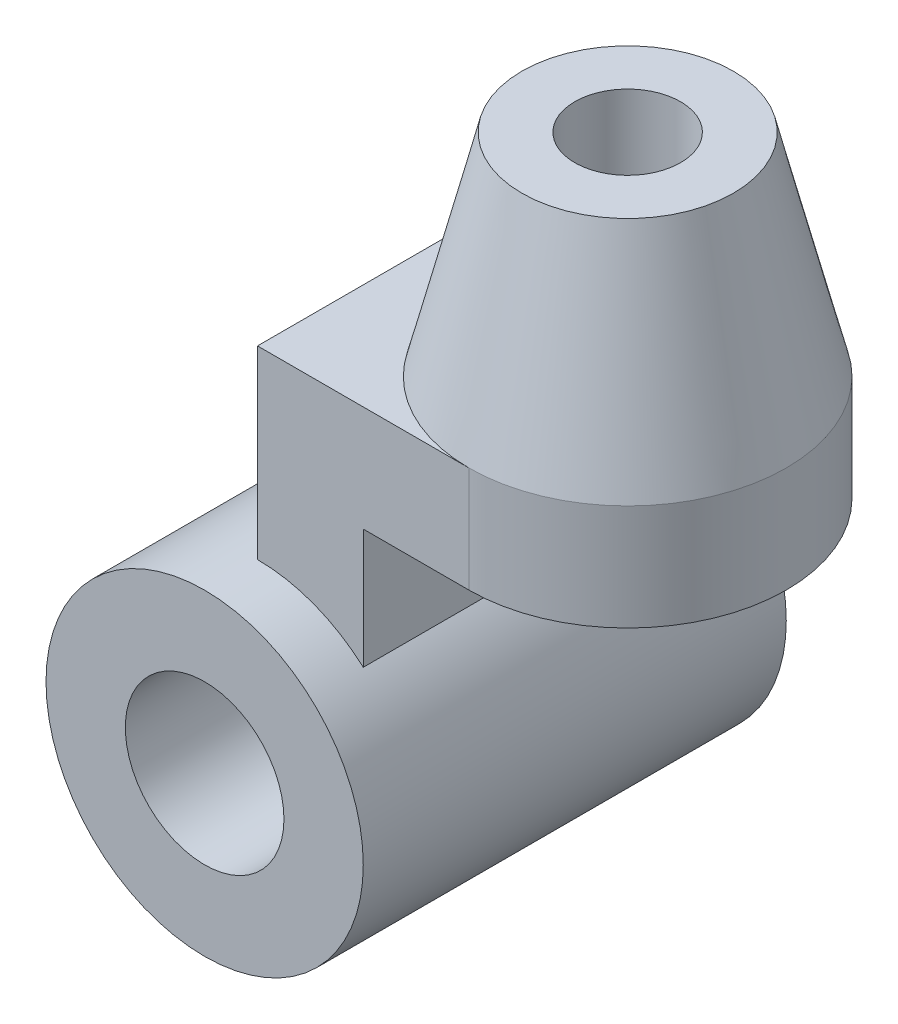
SolidWorks part; units mm, degrees
ref_plane "Front Plane" through (0, 0, 0) normal (0, 0, 1) x (1, 0, 0)
ref_plane "Top Plane" through (0, 0, 0) normal (0, 1, 0) x (1, 0, 0)
ref_plane "Right Plane" through (0, 0, 0) normal (1, 0, 0) x (0, 0, -1)
sketch "Sketch1" plane through (0, 0, 0) normal (0, 0, 1) x (1, 0, 0)
  circle A0 centre (0, 0) radius 300
  circle A1 centre (0, 0) radius 150
  dimension "D1" = 600
  dimension "D2" = 300
extrude "Boss-Extrude1" add sketch "Sketch1" along normal mid plane 800
sketch "Sketch2" plane through (0, 0, 0) normal (0, 0, 1) x (1, 0, 0)
  line L0 (0, 300) -> (0, 650)
  line L1 (0, 650) -> (400, 650)
  line L2 (200, 450) -> (200, 223.6068)
  line L3 (400, 650) -> (400, 450)
  line L4 (400, 450) -> (200, 450)
  circle A0 centre (0, 0) radius 300 construction
  arc A1 (200, 223.6068) -> (0, 300) centre (0, 0) ccw
  dimension "D1" = 350
  dimension "D2" = 200
  dimension "D3" = 400
  dimension "D4" = 200
extrude "Boss-Extrude2" add sketch "Sketch2" along normal mid plane 600
sketch "Sketch5" plane through (0, 0, 0) normal (0, 0, 1) x (1, 0, 0)
  line L0 (400, 1046.5475) -> (400, -75.9294) construction
  line L1 (400, 450) -> (400, 650) construction
  line L2 (500, 1050) -> (500, 450)
  line L3 (500, 450) -> (700, 450)
  line L4 (700, 450) -> (700, 650)
  line L5 (700, 650) -> (600, 1050)
  line L6 (600, 1050) -> (500, 1050)
  line L8 (200, 450) -> (400, 450) construction
  line L9 (400, 650) -> (0, 650) construction
  dimension "D1" = 200
  dimension "D2" = 400
  dimension "D3" = 600
  dimension "D4" = 400
revolve "Revolve1" add sketch "Sketch5" angle 360 about L0
sketch "Sketch6" plane through (0, 650, 0) normal (0, 1, 0) x (1, 0, 0)
  line L0 (400, -100) -> (400, 100) construction
  circle A0 centre (400, 0) radius 100
  dimension "D1" = 200
extrude "Cut-Extrude1" cut sketch "Sketch6" against normal through all
